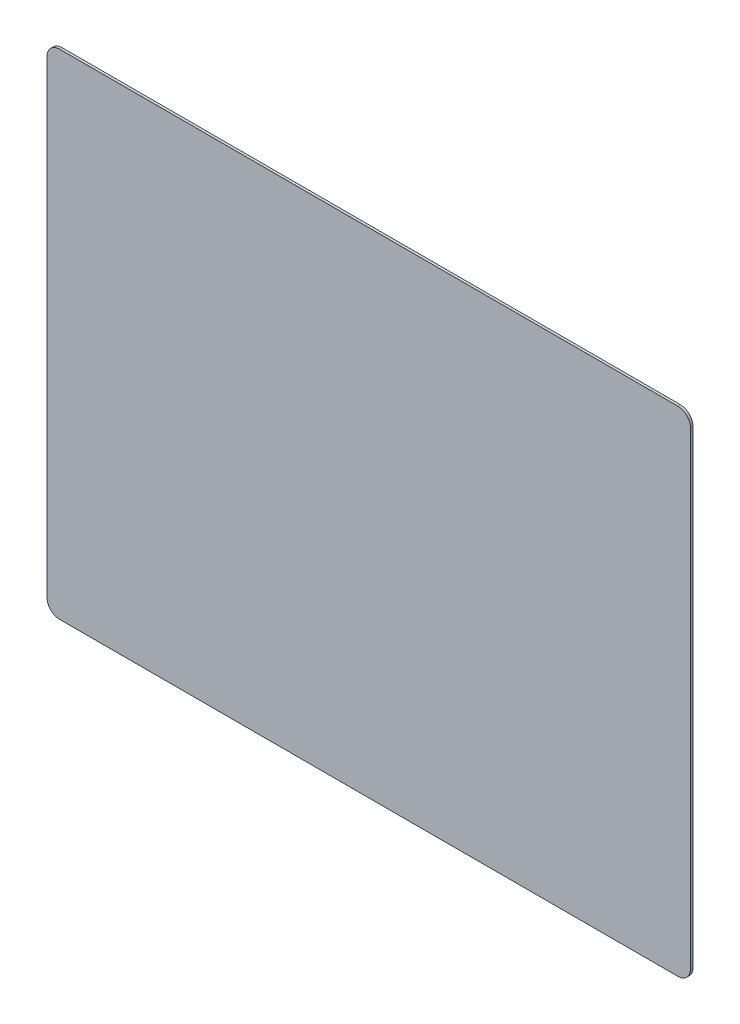
SolidWorks part; units mm, degrees
material "Acrylic (Medium-high impact)"
ref_plane "Front Plane" through (0, 0, 0) normal (0, 0, 1) x (1, 0, 0)
ref_plane "Top Plane" through (0, 0, 0) normal (0, 1, 0) x (1, 0, 0)
ref_plane "Right Plane" through (0, 0, 0) normal (1, 0, 0) x (0, 0, -1)
sketch "Sketch1" plane through (0, 0, 0) normal (0, 0, 1) x (1, 0, 0)
  line L1 (-500, -382.5) -> (500, -382.5) construction
  line L2 (-500, -382.5) -> (-500, 382.5) construction
  line L3 (-500, 382.5) -> (500, 382.5) construction
  line L4 (500, -382.5) -> (500, 382.5) construction
  line L5 (-500, -382.5) -> (500, 382.5) construction
  line L6 (-500, 382.5) -> (500, -382.5) construction
  line L7 (-505, -387.5) -> (505, -387.5)
  line L8 (-505, -387.5) -> (-505, 387.5)
  line L9 (-505, 387.5) -> (505, 387.5)
  line L10 (505, -387.5) -> (505, 387.5)
  line L11 (-505, -387.5) -> (505, 387.5) construction
  line L12 (-505, 387.5) -> (505, -387.5) construction
  point P0 (0, 0)
  dimension "D1" = 1000
  dimension "D2" = 765
  dimension "D3" = 5
  dimension "D4" = 5
extrude "Boss-Extrude1" add sketch "Sketch1" along normal blind 4
fillet "Fillet1" radius 20 4 edges at (-505, -387.5, 2) (-505, 387.5, 2) (505, 387.5, 2) (505, -387.5, 2)
